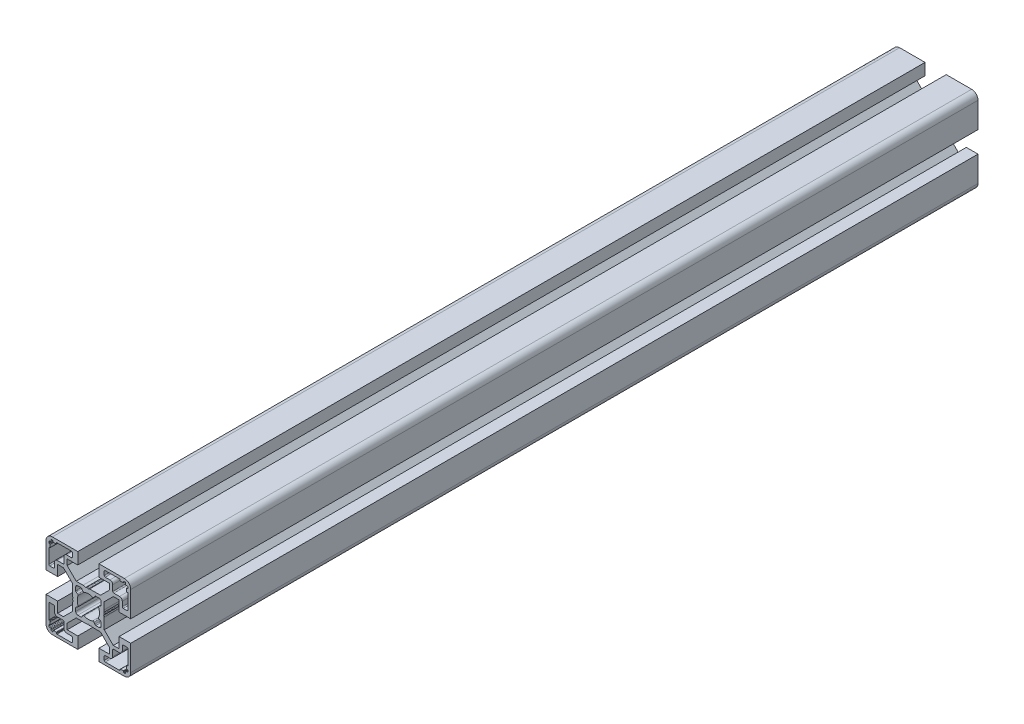
SolidWorks part; units mm, degrees
ref_plane "Front Plane" through (0, 0, 0) normal (0, 0, 1) x (1, 0, 0)
ref_plane "Top Plane" through (0, 0, 0) normal (0, 1, 0) x (1, 0, 0)
ref_plane "Right Plane" through (0, 0, 0) normal (1, 0, 0) x (0, 0, -1)
sketch "Sketch1" plane through (0, 0, 0) normal (0, 0, 1) x (1, 0, 0)
  line L0 (-11.7678, -10) -> (-14.5, -10)
  line L1 (-14.5, -10) -> (-14.5, -5)
  line L2 (-14.5, -5) -> (-20, -5)
  line L3 (-20, -5) -> (-20, -17)
  line L4 (-17, -20) -> (-5, -20)
  line L5 (-5, -20) -> (-5, -14.5)
  line L6 (-5, -14.5) -> (-10, -14.5)
  line L7 (-10, -14.5) -> (-10, -11.7678)
  line L8 (-10, -11.7678) -> (-5.7322, -7.5)
  line L9 (-5.7322, -7.5) -> (-0.6536, -7.5)
  line L10 (-0.4036, -7.433) -> (0, -7.2)
  line L11 (0, -7.2) -> (0.4036, -7.433)
  line L12 (0.9036, -7.433) -> (1.2189, -7.251)
  line L13 (1.2189, -7.251) -> (2.5, -7.5)
  line L14 (2.5, -7.5) -> (5.7322, -7.5)
  line L15 (5.7322, -7.5) -> (10, -11.7678)
  line L16 (10, -11.7678) -> (10, -14.5)
  line L17 (10, -14.5) -> (5, -14.5)
  line L18 (5, -14.5) -> (5, -20)
  line L19 (5, -20) -> (17, -20)
  line L20 (20, -17) -> (20, -5)
  line L21 (20, -5) -> (14.5, -5)
  line L22 (14.5, -5) -> (14.5, -10)
  line L23 (14.5, -10) -> (11.7678, -10)
  line L24 (11.7678, -10) -> (7.5, -5.7322)
  line L25 (7.5, -5.7322) -> (7.5, -0.6536)
  line L26 (7.433, -0.4036) -> (7.2, 0)
  line L27 (7.2, 0) -> (7.433, 0.4036)
  line L28 (7.433, 0.9036) -> (7.251, 1.2189)
  line L29 (7.251, 1.2189) -> (7.5, 2.5)
  line L30 (7.5, 2.5) -> (7.5, 5.7322)
  line L31 (7.5, 5.7322) -> (11.7678, 10)
  line L32 (11.7678, 10) -> (14.5, 10)
  line L33 (14.5, 10) -> (14.5, 5)
  line L34 (14.5, 5) -> (20, 5)
  line L35 (20, 5) -> (20, 17)
  line L36 (17, 20) -> (5, 20)
  line L37 (5, 20) -> (5, 14.5)
  line L38 (5, 14.5) -> (10, 14.5)
  line L39 (10, 14.5) -> (10, 11.7678)
  line L40 (10, 11.7678) -> (5.7322, 7.5)
  line L41 (5.7322, 7.5) -> (0.6536, 7.5)
  line L42 (0.4036, 7.433) -> (0, 7.2)
  line L43 (0, 7.2) -> (-0.4036, 7.433)
  line L44 (-0.9036, 7.433) -> (-1.2189, 7.251)
  line L45 (-1.2189, 7.251) -> (-2.5, 7.5)
  line L46 (-2.5, 7.5) -> (-5.7322, 7.5)
  line L47 (-5.7322, 7.5) -> (-10, 11.7678)
  line L48 (-10, 11.7678) -> (-10, 14.5)
  line L49 (-10, 14.5) -> (-5, 14.5)
  line L50 (-5, 14.5) -> (-5, 20)
  line L51 (-5, 20) -> (-17, 20)
  line L52 (-20, 17) -> (-20, 5)
  line L53 (-20, 5) -> (-14.5, 5)
  line L54 (-14.5, 5) -> (-14.5, 10)
  line L55 (-14.5, 10) -> (-11.7678, 10)
  line L56 (-11.7678, 10) -> (-7.5, 5.7322)
  line L57 (-7.5, 5.7322) -> (-7.5, 0.6536)
  line L58 (-7.433, 0.4036) -> (-7.2, 0)
  line L59 (-7.2, 0) -> (-7.433, -0.4036)
  line L60 (-7.433, -0.9036) -> (-7.251, -1.2189)
  line L61 (-7.251, -1.2189) -> (-7.5, -2.5)
  line L62 (-7.5, -2.5) -> (-7.5, -5.7322)
  line L63 (-7.5, -5.7322) -> (-11.7678, -10)
  line L64 (7.5, 16.5) -> (7.5, 18.2)
  line L65 (8, 18.7) -> (14.8, 18.7)
  line L66 (15, 18.5) -> (15, 18.2)
  line L67 (15.2, 18) -> (16.4, 18)
  line L68 (16.6, 18.2) -> (16.6, 18.5)
  line L69 (16.8, 18.7) -> (17.3, 18.7)
  line L70 (17.6, 18.4) -> (17.6, 17.9)
  line L71 (17.9, 17.6) -> (18.4, 17.6)
  line L72 (18.7, 17.3) -> (18.7, 16.8)
  line L73 (18.5, 16.6) -> (18.2, 16.6)
  line L74 (18, 16.4) -> (18, 15.2)
  line L75 (18.2, 15) -> (18.5, 15)
  line L76 (18.7, 14.8) -> (18.7, 8)
  line L77 (18.2, 7.5) -> (16.5, 7.5)
  line L78 (16, 8) -> (16, 10.2)
  line L79 (14.7, 11.5) -> (12, 11.5)
  line L80 (11.5, 12) -> (11.5, 14.7)
  line L81 (10.2, 16) -> (8, 16)
  line L82 (14.8, -18.7) -> (8, -18.7)
  line L83 (7.5, -18.2) -> (7.5, -16.5)
  line L84 (8, -16) -> (10.2, -16)
  line L85 (11.5, -14.7) -> (11.5, -12)
  line L86 (12, -11.5) -> (14.7, -11.5)
  line L87 (16, -10.2) -> (16, -8)
  line L88 (16.5, -7.5) -> (18.2, -7.5)
  line L89 (18.7, -8) -> (18.7, -14.8)
  line L90 (18.5, -15) -> (18.2, -15)
  line L91 (18, -15.2) -> (18, -16.4)
  line L92 (18.2, -16.6) -> (18.5, -16.6)
  line L93 (18.7, -16.8) -> (18.7, -17.3)
  line L94 (18.4, -17.6) -> (17.9, -17.6)
  line L95 (17.6, -17.9) -> (17.6, -18.4)
  line L96 (17.3, -18.7) -> (16.8, -18.7)
  line L97 (16.6, -18.5) -> (16.6, -18.2)
  line L98 (16.4, -18) -> (15.2, -18)
  line L99 (15, -18.2) -> (15, -18.5)
  line L100 (-18.7, 16.8) -> (-18.7, 17.3)
  line L101 (-18.4, 17.6) -> (-17.9, 17.6)
  line L102 (-17.6, 17.9) -> (-17.6, 18.4)
  line L103 (-17.3, 18.7) -> (-16.8, 18.7)
  line L104 (-16.6, 18.5) -> (-16.6, 18.2)
  line L105 (-16.4, 18) -> (-15.2, 18)
  line L106 (-15, 18.2) -> (-15, 18.5)
  line L107 (-14.8, 18.7) -> (-8, 18.7)
  line L108 (-7.5, 18.2) -> (-7.5, 16.5)
  line L109 (-8, 16) -> (-10.2, 16)
  line L110 (-11.5, 14.7) -> (-11.5, 12)
  line L111 (-12, 11.5) -> (-14.7, 11.5)
  line L112 (-16, 10.2) -> (-16, 8)
  line L113 (-16.5, 7.5) -> (-18.2, 7.5)
  line L114 (-18.7, 8) -> (-18.7, 14.8)
  line L115 (-18.5, 15) -> (-18.2, 15)
  line L116 (-18, 15.2) -> (-18, 16.4)
  line L117 (-18.2, 16.6) -> (-18.5, 16.6)
  line L118 (-18.7, -14.8) -> (-18.7, -8)
  line L119 (-18.2, -7.5) -> (-16.5, -7.5)
  line L120 (-16, -8) -> (-16, -10.2)
  line L121 (-14.7, -11.5) -> (-12, -11.5)
  line L122 (-11.5, -12) -> (-11.5, -14.7)
  line L123 (-10.2, -16) -> (-8, -16)
  line L124 (-7.5, -16.5) -> (-7.5, -18.2)
  line L125 (-8, -18.7) -> (-14.8, -18.7)
  line L126 (-15, -18.5) -> (-15, -18.2)
  line L127 (-15.2, -18) -> (-16.4, -18)
  line L128 (-16.6, -18.2) -> (-16.6, -18.5)
  line L129 (-16.8, -18.7) -> (-17.3, -18.7)
  line L130 (-17.6, -18.4) -> (-17.6, -17.9)
  line L131 (-17.9, -17.6) -> (-18.4, -17.6)
  line L132 (-18.7, -17.3) -> (-18.7, -16.8)
  line L133 (-18.5, -16.6) -> (-18.2, -16.6)
  line L134 (-18, -16.4) -> (-18, -15.2)
  line L135 (-18.2, -15) -> (-18.5, -15)
  line L136 (-6, 3.4907) -> (-6, 5)
  line L137 (-5, 6) -> (-3.4907, 6)
  line L138 (-3.0492, 5.7347) -> (-2.6892, 5.0577)
  line L139 (2.6892, 5.0577) -> (3.0492, 5.7347)
  line L140 (3.4907, 6) -> (5, 6)
  line L141 (6, 5) -> (6, 3.4907)
  line L142 (5.7347, 3.0492) -> (5.0577, 2.6892)
  line L143 (5.0577, -2.6892) -> (5.7347, -3.0492)
  line L144 (6, -3.4907) -> (6, -5)
  line L145 (5, -6) -> (3.4907, -6)
  line L146 (3.0492, -5.7347) -> (2.6892, -5.0577)
  line L147 (-2.6892, -5.0577) -> (-3.0492, -5.7347)
  line L148 (-3.4907, -6) -> (-5, -6)
  line L149 (-6, -5) -> (-6, -3.4907)
  line L150 (-5.7347, -3.0492) -> (-5.0577, -2.6892)
  line L151 (-5.0577, 2.6892) -> (-5.7347, 3.0492)
  arc A0 (-20, -17) -> (-17, -20) centre (-17, -17) ccw
  arc A1 (-0.6536, -7.5) -> (-0.4036, -7.433) centre (-0.6536, -7) ccw
  arc A2 (0.4036, -7.433) -> (0.9036, -7.433) centre (0.6536, -7) ccw
  arc A3 (17, -20) -> (20, -17) centre (17, -17) ccw
  arc A4 (7.5, -0.6536) -> (7.433, -0.4036) centre (7, -0.6536) ccw
  arc A5 (7.433, 0.4036) -> (7.433, 0.9036) centre (7, 0.6536) ccw
  arc A6 (20, 17) -> (17, 20) centre (17, 17) ccw
  arc A7 (0.6536, 7.5) -> (0.4036, 7.433) centre (0.6536, 7) ccw
  arc A8 (-0.4036, 7.433) -> (-0.9036, 7.433) centre (-0.6536, 7) ccw
  arc A9 (-17, 20) -> (-20, 17) centre (-17, 17) ccw
  arc A10 (-7.5, 0.6536) -> (-7.433, 0.4036) centre (-7, 0.6536) ccw
  arc A11 (-7.433, -0.4036) -> (-7.433, -0.9036) centre (-7, -0.6536) ccw
  arc A12 (8, 16) -> (7.5, 16.5) centre (8, 16.5) cw
  arc A13 (7.5, 18.2) -> (8, 18.7) centre (8, 18.2) cw
  arc A14 (14.8, 18.7) -> (15, 18.5) centre (14.8, 18.5) cw
  arc A15 (15, 18.2) -> (15.2, 18) centre (15.2, 18.2) ccw
  arc A16 (16.4, 18) -> (16.6, 18.2) centre (16.4, 18.2) ccw
  arc A17 (16.6, 18.5) -> (16.8, 18.7) centre (16.8, 18.5) cw
  arc A18 (17.3, 18.7) -> (17.6, 18.4) centre (17.3, 18.4) cw
  arc A19 (17.6, 17.9) -> (17.9, 17.6) centre (17.9, 17.9) ccw
  arc A20 (18.4, 17.6) -> (18.7, 17.3) centre (18.4, 17.3) cw
  arc A21 (18.7, 16.8) -> (18.5, 16.6) centre (18.5, 16.8) cw
  arc A22 (18.2, 16.6) -> (18, 16.4) centre (18.2, 16.4) ccw
  arc A23 (18, 15.2) -> (18.2, 15) centre (18.2, 15.2) ccw
  arc A24 (18.5, 15) -> (18.7, 14.8) centre (18.5, 14.8) cw
  arc A25 (18.7, 8) -> (18.2, 7.5) centre (18.2, 8) cw
  arc A26 (16.5, 7.5) -> (16, 8) centre (16.5, 8) cw
  arc A27 (16, 10.2) -> (14.7, 11.5) centre (14.7, 10.2) ccw
  arc A28 (12, 11.5) -> (11.5, 12) centre (12, 12) cw
  arc A29 (11.5, 14.7) -> (10.2, 16) centre (10.2, 14.7) ccw
  arc A30 (8, -18.7) -> (7.5, -18.2) centre (8, -18.2) cw
  arc A31 (7.5, -16.5) -> (8, -16) centre (8, -16.5) cw
  arc A32 (10.2, -16) -> (11.5, -14.7) centre (10.2, -14.7) ccw
  arc A33 (11.5, -12) -> (12, -11.5) centre (12, -12) cw
  arc A34 (14.7, -11.5) -> (16, -10.2) centre (14.7, -10.2) ccw
  arc A35 (16, -8) -> (16.5, -7.5) centre (16.5, -8) cw
  arc A36 (18.2, -7.5) -> (18.7, -8) centre (18.2, -8) cw
  arc A37 (18.7, -14.8) -> (18.5, -15) centre (18.5, -14.8) cw
  arc A38 (18.2, -15) -> (18, -15.2) centre (18.2, -15.2) ccw
  arc A39 (18, -16.4) -> (18.2, -16.6) centre (18.2, -16.4) ccw
  arc A40 (18.5, -16.6) -> (18.7, -16.8) centre (18.5, -16.8) cw
  arc A41 (18.7, -17.3) -> (18.4, -17.6) centre (18.4, -17.3) cw
  arc A42 (17.9, -17.6) -> (17.6, -17.9) centre (17.9, -17.9) ccw
  arc A43 (17.6, -18.4) -> (17.3, -18.7) centre (17.3, -18.4) cw
  arc A44 (16.8, -18.7) -> (16.6, -18.5) centre (16.8, -18.5) cw
  arc A45 (16.6, -18.2) -> (16.4, -18) centre (16.4, -18.2) ccw
  arc A46 (15.2, -18) -> (15, -18.2) centre (15.2, -18.2) ccw
  arc A47 (15, -18.5) -> (14.8, -18.7) centre (14.8, -18.5) cw
  arc A48 (-18.5, 16.6) -> (-18.7, 16.8) centre (-18.5, 16.8) cw
  arc A49 (-18.7, 17.3) -> (-18.4, 17.6) centre (-18.4, 17.3) cw
  arc A50 (-17.9, 17.6) -> (-17.6, 17.9) centre (-17.9, 17.9) ccw
  arc A51 (-17.6, 18.4) -> (-17.3, 18.7) centre (-17.3, 18.4) cw
  arc A52 (-16.8, 18.7) -> (-16.6, 18.5) centre (-16.8, 18.5) cw
  arc A53 (-16.6, 18.2) -> (-16.4, 18) centre (-16.4, 18.2) ccw
  arc A54 (-15.2, 18) -> (-15, 18.2) centre (-15.2, 18.2) ccw
  arc A55 (-15, 18.5) -> (-14.8, 18.7) centre (-14.8, 18.5) cw
  arc A56 (-8, 18.7) -> (-7.5, 18.2) centre (-8, 18.2) cw
  arc A57 (-7.5, 16.5) -> (-8, 16) centre (-8, 16.5) cw
  arc A58 (-10.2, 16) -> (-11.5, 14.7) centre (-10.2, 14.7) ccw
  arc A59 (-11.5, 12) -> (-12, 11.5) centre (-12, 12) cw
  arc A60 (-14.7, 11.5) -> (-16, 10.2) centre (-14.7, 10.2) ccw
  arc A61 (-16, 8) -> (-16.5, 7.5) centre (-16.5, 8) cw
  arc A62 (-18.2, 7.5) -> (-18.7, 8) centre (-18.2, 8) cw
  arc A63 (-18.7, 14.8) -> (-18.5, 15) centre (-18.5, 14.8) cw
  arc A64 (-18.2, 15) -> (-18, 15.2) centre (-18.2, 15.2) ccw
  arc A65 (-18, 16.4) -> (-18.2, 16.6) centre (-18.2, 16.4) ccw
  arc A66 (-18.5, -15) -> (-18.7, -14.8) centre (-18.5, -14.8) cw
  arc A67 (-18.7, -8) -> (-18.2, -7.5) centre (-18.2, -8) cw
  arc A68 (-16.5, -7.5) -> (-16, -8) centre (-16.5, -8) cw
  arc A69 (-16, -10.2) -> (-14.7, -11.5) centre (-14.7, -10.2) ccw
  arc A70 (-12, -11.5) -> (-11.5, -12) centre (-12, -12) cw
  arc A71 (-11.5, -14.7) -> (-10.2, -16) centre (-10.2, -14.7) ccw
  arc A72 (-8, -16) -> (-7.5, -16.5) centre (-8, -16.5) cw
  arc A73 (-7.5, -18.2) -> (-8, -18.7) centre (-8, -18.2) cw
  arc A74 (-14.8, -18.7) -> (-15, -18.5) centre (-14.8, -18.5) cw
  arc A75 (-15, -18.2) -> (-15.2, -18) centre (-15.2, -18.2) ccw
  arc A76 (-16.4, -18) -> (-16.6, -18.2) centre (-16.4, -18.2) ccw
  arc A77 (-16.6, -18.5) -> (-16.8, -18.7) centre (-16.8, -18.5) cw
  arc A78 (-17.3, -18.7) -> (-17.6, -18.4) centre (-17.3, -18.4) cw
  arc A79 (-17.6, -17.9) -> (-17.9, -17.6) centre (-17.9, -17.9) ccw
  arc A80 (-18.4, -17.6) -> (-18.7, -17.3) centre (-18.4, -17.3) cw
  arc A81 (-18.7, -16.8) -> (-18.5, -16.6) centre (-18.5, -16.8) cw
  arc A82 (-18.2, -16.6) -> (-18, -16.4) centre (-18.2, -16.4) ccw
  arc A83 (-18, -15.2) -> (-18.2, -15) centre (-18.2, -15.2) ccw
  arc A84 (-5.7347, 3.0492) -> (-6, 3.4907) centre (-5.5, 3.4907) cw
  arc A85 (-6, 5) -> (-5, 6) centre (-5, 5) cw
  arc A86 (-3.4907, 6) -> (-3.0492, 5.7347) centre (-3.4907, 5.5) cw
  arc A87 (-2.6892, 5.0577) -> (-2.0523, 4.8322) centre (-2.2478, 5.2925) ccw
  arc A88 (-2.0523, 4.8322) -> (2.0523, 4.8322) centre (0, 0) cw
  arc A89 (2.0523, 4.8322) -> (2.6892, 5.0577) centre (2.2478, 5.2925) ccw
  arc A90 (3.0492, 5.7347) -> (3.4907, 6) centre (3.4907, 5.5) cw
  arc A91 (5, 6) -> (6, 5) centre (5, 5) cw
  arc A92 (6, 3.4907) -> (5.7347, 3.0492) centre (5.5, 3.4907) cw
  arc A93 (5.0577, 2.6892) -> (4.8322, 2.0523) centre (5.2925, 2.2478) ccw
  arc A94 (4.8322, 2.0523) -> (4.8322, -2.0523) centre (0, 0) cw
  arc A95 (4.8322, -2.0523) -> (5.0577, -2.6892) centre (5.2925, -2.2478) ccw
  arc A96 (5.7347, -3.0492) -> (6, -3.4907) centre (5.5, -3.4907) cw
  arc A97 (6, -5) -> (5, -6) centre (5, -5) cw
  arc A98 (3.4907, -6) -> (3.0492, -5.7347) centre (3.4907, -5.5) cw
  arc A99 (2.6892, -5.0577) -> (2.0523, -4.8322) centre (2.2478, -5.2925) ccw
  arc A100 (2.0523, -4.8322) -> (-2.0523, -4.8322) centre (0, 0) cw
  arc A101 (-2.0523, -4.8322) -> (-2.6892, -5.0577) centre (-2.2478, -5.2925) ccw
  arc A102 (-3.0492, -5.7347) -> (-3.4907, -6) centre (-3.4907, -5.5) cw
  arc A103 (-5, -6) -> (-6, -5) centre (-5, -5) cw
  arc A104 (-6, -3.4907) -> (-5.7347, -3.0492) centre (-5.5, -3.4907) cw
  arc A105 (-5.0577, -2.6892) -> (-4.8322, -2.0523) centre (-5.2925, -2.2478) ccw
  arc A106 (-4.8322, -2.0523) -> (-4.8322, 2.0523) centre (0, 0) cw
  arc A107 (-4.8322, 2.0523) -> (-5.0577, 2.6892) centre (-5.2925, 2.2478) ccw
extrude "Boss-Extrude1" add sketch "Sketch1" against normal blind 400
